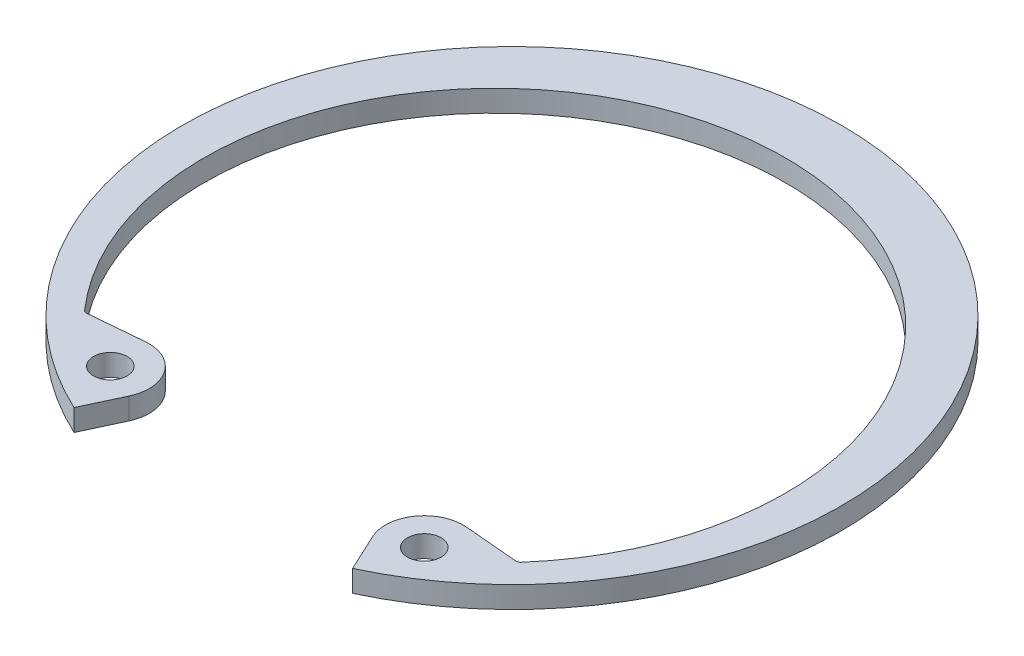
SolidWorks part; units mm, degrees
material "Cast Carbon Steel"
ref_plane "Front" through (0, 0, 0) normal (0, 0, 1) x (1, 0, 0)
ref_plane "Top" through (0, 0, 0) normal (0, 1, 0) x (1, 0, 0)
ref_plane "Right" through (0, 0, 0) normal (1, 0, 0) x (0, 0, -1)
sketch "Sketch2" plane through (0, 0, 0) normal (0, 1, 0) x (1, 0, 0)
  line L0 (0, 0) -> (0, -19.3802) construction
  line L1 (-12.7426, -12.3998) -> (-13.8894, -13.5158) construction
  line L2 (8.1904, -17.5644) -> (7.1594, -15.3534)
  line L3 (-8.1904, -17.5644) -> (-7.1594, -15.3534)
  line L4 (0, 16.0782) -> (0, 19.3802) construction
  line L5 (12.7426, -12.3998) -> (9.4305, -12.11)
  line L6 (-12.7426, -12.3998) -> (-9.4305, -12.11)
  line L7 (7.9968, -12.4633) -> (-0.764, -18.0844) construction
  line L8 (-0.764, -18.0844) -> (1.705, -21.9325) construction
  line L9 (1.705, -21.9325) -> (10.4657, -16.3114) construction
  line L10 (7.9968, -12.4633) -> (10.4657, -16.3114) construction
  line L11 (9.2313, -14.3873) -> (7.1594, -15.3534) construction
  line L12 (9.2313, -14.3873) -> (10.4657, -16.3114) construction
  line L13 (7.9968, -12.4633) -> (-7.9968, -12.4633) construction
  line L14 (-7.9968, -12.4633) -> (-10.4657, -16.3114) construction
  line L15 (-19.3802, 0) -> (19.3802, 0) construction
  arc A1 (8.1904, -17.5644) -> (-8.1904, -17.5644) centre (0, 0) ccw
  arc A2 (12.7426, -12.3998) -> (-12.7426, -12.3998) centre (0, -1.0117) ccw
  circle A3 centre (0, 0) radius 19.3802 construction
  arc A4 (7.1594, -15.3534) -> (9.4305, -12.11) centre (9.2313, -14.3873) cw
  arc A5 (-7.1594, -15.3534) -> (-9.4305, -12.11) centre (-9.2313, -14.3873) ccw
  circle A6 centre (9.2313, -14.3873) radius 0.9906
  circle A7 centre (-9.2313, -14.3873) radius 0.9906
  arc A8 (12.7426, -12.3998) -> (-12.7426, -12.3998) centre (0, -1.0117) cw construction
  circle A9 centre (0, 0) radius 13.081 construction
  point P5 (9.2313, -14.3873)
  point P10 (7.9968, -12.4633)
  dimension "D1" = 60
  dimension "D2" = 60
  dimension "L" = 26.162
  dimension "R" = 1.9812
  dimension "Df" = 38.7604
  dimension "H" = 4.572
  dimension "Angle" = 25
  dimension "Sec. Max" = 3.302
  dimension "Sec. Min" = 1.6002
extrude "Extrude1" add sketch "Sketch2" against normal blind 1.27
fillet "Fillet1" radius 0.254 2 edges at (-12.7426, -0.635, 12.3998) (12.7426, -0.635, 12.3998)
sketch "Sketch3" plane through (0, 0, 0) normal (1, 0, 0) x (0, 0, -1)
  line L0 (-17.4625, -13.2588) -> (-17.4625, -1.3462)
  line L1 (-17.4625, -1.3462) -> (-18.5547, -1.3462)
  line L2 (-18.5547, -1.3462) -> (-18.5547, 0.0762)
  line L3 (-18.5547, 0.0762) -> (-17.4625, 0.0762)
  line L4 (-17.4625, 0.0762) -> (-17.4625, 1.9812)
  line L5 (-17.4625, -13.2588) -> (-19.6469, -13.2588)
  line L6 (-17.4625, -1.3462) -> (0, -1.3462) construction
  line L7 (-17.4625, 1.9812) -> (-19.6469, 1.9812)
  line L8 (0, 130.3401) -> (0, 164.6301) construction
  line L9 (0, -1.3462) -> (0, 0.0762) construction
  line L10 (0, 0.0762) -> (-17.4625, 0.0762) construction
  line L11 (-18.5547, -0.635) -> (0, -0.635) construction
  line L12 (0, -135.0899) -> (0, 130.3401) construction
  line L13 (-12.3035, -1.27) -> (16.0782, -1.27) construction
  line L14 (-19.6469, -13.2588) -> (-19.6469, 1.9812)
  dimension "D1" = 0.635
  dimension "Shaft Lg" = 15.24
  dimension "Dg" = 37.1094
  dimension "Db" = 34.925
  dimension "W" = 1.4224
  dimension "D2" = 1.0922
  dimension "D3" = 1.905
  dimension "D4" = 1.0922
revolve "Revolve1" [suppressed] add sketch "Sketch3" angle 360 about L8
delete or keep bodies "Body-Delete1" [suppressed] type delete bodies bodies 116
equation "\"D3@Sketch3\" = \"Shaft Lg@Sketch3\"/8"
equation "\"Shaft Lg@Sketch3\" = \"D1@Extrude1\"*12"
equation "\"D1@Sketch3\" = \"D1@Extrude1\"/2"
equation "\"D2@Sketch3\" = \"D4@Sketch3\""
